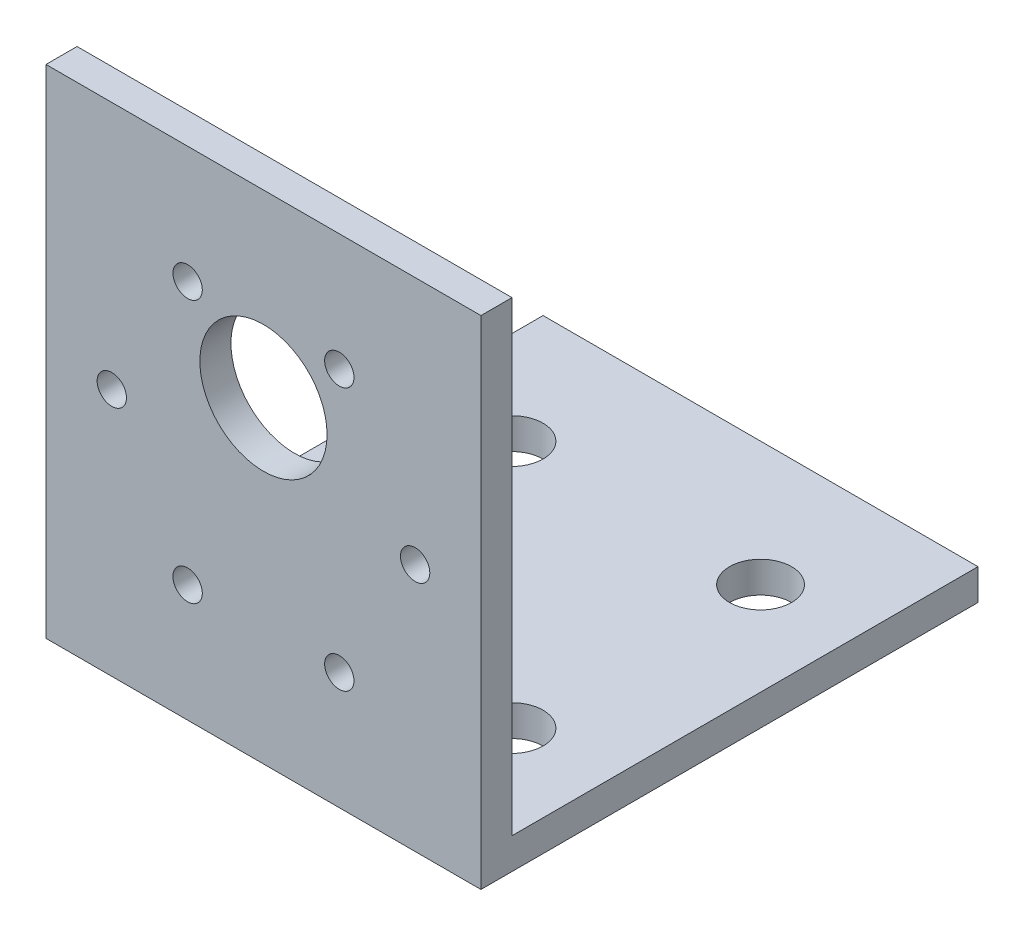
SolidWorks part; units mm, degrees
ref_plane "Front Plane" through (0, 0, 0) normal (0, 0, 1) x (1, 0, 0)
ref_plane "Top Plane" through (0, 0, 0) normal (0, 1, 0) x (1, 0, 0)
ref_plane "Right Plane" through (0, 0, 0) normal (1, 0, 0) x (0, 0, -1)
sketch "Sketch1" plane through (0, 0, 0) normal (0, 0, 1) x (1, 0, 0)
  line L0 (22.225, 50.8) -> (22.225, 0) construction
  line L1 (0, 0) -> (44.45, 0)
  line L2 (0, 0) -> (0, 50.8)
  line L3 (0, 50.8) -> (44.45, 50.8)
  line L4 (44.45, 0) -> (44.45, 50.8)
  line L5 (-22.225, 25.4) -> (66.675, 25.4) construction
  line L6 (22.225, 25.4) -> (54.2263, 80.8279) construction
  line L7 (22.225, 25.4) -> (59.5166, -39.1909) construction
  circle A0 centre (22.225, 32.4) radius 6.5
  circle A1 centre (22.225, 25.4) radius 18.5 construction
  circle A2 centre (6.725, 25.4) radius 1.5
  circle A3 centre (37.725, 25.4) radius 1.5
  circle A4 centre (29.975, 11.9766) radius 1.5
  circle A5 centre (14.475, 11.9766) radius 1.5
  circle A6 centre (14.475, 38.8234) radius 1.5
  circle A7 centre (29.975, 38.8234) radius 1.5
  circle A8 centre (22.225, 25.4) radius 15.5 construction
  dimension "D3" = 13
  dimension "D4" = 37
  dimension "D7" = 3
  dimension "D10" = 31
  dimension "D1" = 44.45
  dimension "D2" = 50.8
  dimension "D5" = 7
  dimension "D6" = 25.4
  dimension "D8" = 60
  dimension "D9" = 60
extrude "Boss-Extrude1" add sketch "Sketch1" along normal blind 3.175
sketch "Sketch2" plane through (0, 0, 0) normal (0, 0, -1) x (-1, 0, 0)
  line L0 (0, 50.8) -> (0, 0) construction
  line L1 (-44.45, 0) -> (0, 0)
  line L2 (-44.45, 0) -> (-44.45, 3.175)
  line L3 (-44.45, 3.175) -> (0, 3.175)
  line L4 (0, 0) -> (0, 3.175)
  dimension "D1" = 3.175
extrude "Boss-Extrude2" add sketch "Sketch2" along normal blind 47.625
sketch "Sketch3" plane through (0, 3.175, 0) normal (0, 1, 0) x (1, 0, 0)
  line L0 (44.45, 47.625) -> (44.45, 0) construction
  line L1 (0, 0) -> (44.45, 0) construction
  circle A0 centre (34.925, 9.525) radius 3.175
  circle A1 centre (34.925, 34.925) radius 3.175
  circle A2 centre (9.525, 9.525) radius 3.175
  circle A3 centre (9.525, 34.925) radius 3.175
  dimension "D3" = 6.35
  dimension "D5" = 9.525
  dimension "D1" = 25.4
  dimension "D2" = 25.4
  dimension "D4" = 9.525
extrude "Cut-Extrude1" cut sketch "Sketch3" against normal through all
